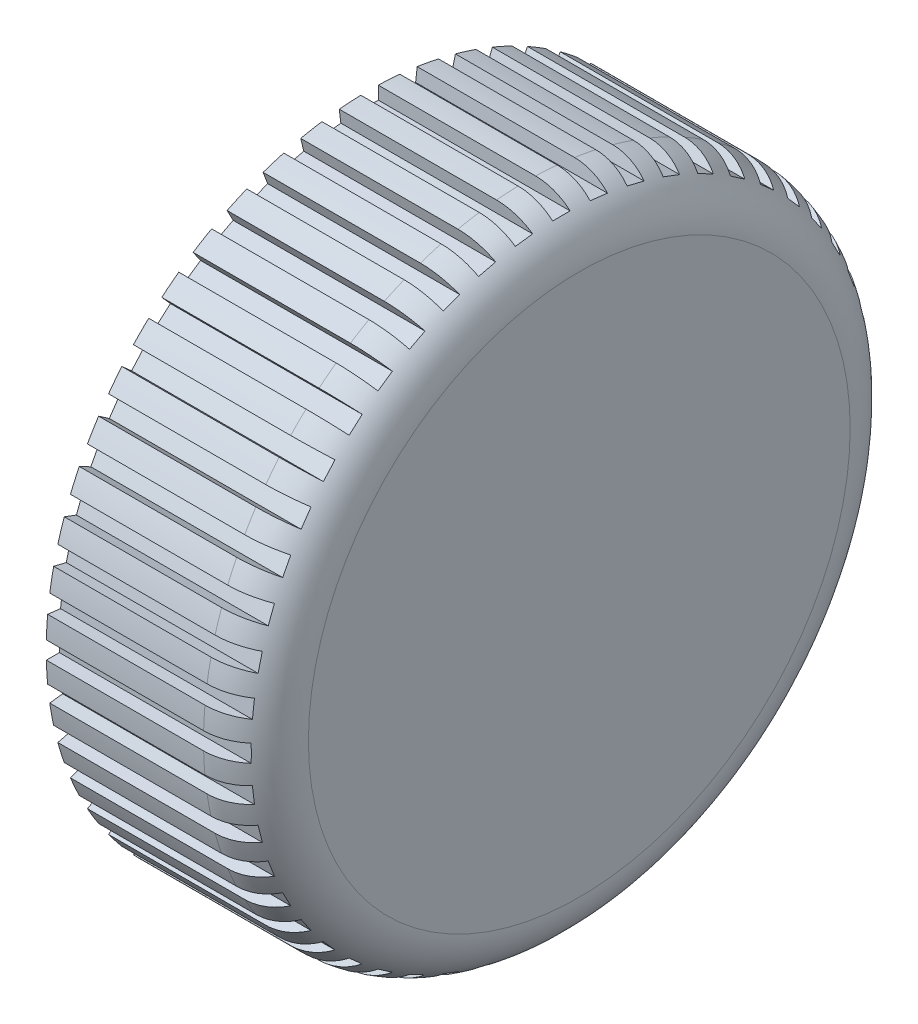
SolidWorks part; units mm, degrees
ref_plane "Спереди" through (0, 0, 0) normal (0, 0, 1) x (1, 0, 0)
ref_plane "Сверху" through (0, 0, 0) normal (0, 1, 0) x (1, 0, 0)
ref_plane "Справа" through (0, 0, 0) normal (1, 0, 0) x (0, 0, -1)
sketch "Эскиз1" plane through (0, 0, 0) normal (0, 0, 1) x (1, 0, 0)
  line L0 (0, 37) -> (0, 30.3)
  line L1 (0, 30.3) -> (16, 30.3)
  line L2 (16, 30.3) -> (16, 0)
  line L3 (16, 0) -> (24, 0)
  line L4 (24, 0) -> (24, 31)
  line L5 (18, 37) -> (0, 37)
  line L6 (0, 30.3) -> (0, 0) construction
  line L7 (0, 0) -> (16, 0) construction
  arc A0 (24, 31) -> (18, 37) centre (18, 31) ccw
  point P11 (0, 0)
  point P12 (0, 0)
  point P13 (0, 0)
  point P14 (16, 0)
  point P15 (16, 0.8492)
  dimension "D6" = 6
  dimension "D1" = 60.6
  dimension "D2" = 74
  dimension "D3" = 8
  dimension "D4" = 16
revolve "Повернуть1" add sketch "Эскиз1" angle 360 about L7
sketch "Эскиз2" plane through (0, 0, 0) normal (-1, 0, 0) x (0, 0, 1)
  line L0 (0, 35.5) -> (0, 0) construction
  line L1 (-1, 38.5) -> (1, 38.5)
  line L2 (-1, 38.5) -> (-1, 35.5)
  line L3 (-1, 35.5) -> (1, 35.5)
  line L4 (1, 38.5) -> (1, 35.5)
  line L5 (5.6334, 38.0988) -> (5.2718, 35.1206)
  line L6 (3.648, 38.3398) -> (3.2863, 35.3617)
  line L7 (3.648, 38.3398) -> (5.6334, 38.0988)
  line L8 (3.2863, 35.3617) -> (5.2718, 35.1206)
  line L9 (10.1846, 37.1419) -> (9.4666, 34.2291)
  line L10 (8.2427, 37.6206) -> (7.5248, 34.7078)
  line L11 (8.2427, 37.6206) -> (10.1846, 37.1419)
  line L12 (7.5248, 34.7078) -> (9.4666, 34.2291)
  line L13 (14.5873, 35.6435) -> (13.5235, 32.8385)
  line L14 (12.7173, 36.3527) -> (11.6535, 33.5477)
  line L15 (12.7173, 36.3527) -> (14.5873, 35.6435)
  line L16 (11.6535, 33.5477) -> (13.5235, 32.8385)
  line L17 (18.7773, 33.6253) -> (17.3831, 30.969)
  line L18 (17.0064, 34.5548) -> (15.6122, 31.8984)
  line L19 (17.0064, 34.5548) -> (18.7773, 33.6253)
  line L20 (15.6122, 31.8984) -> (17.3831, 30.969)
  line L21 (22.6935, 31.1168) -> (20.9893, 28.6479)
  line L22 (21.0475, 32.2529) -> (19.3433, 29.784)
  line L23 (21.0475, 32.2529) -> (22.6935, 31.1168)
  line L24 (19.3433, 29.784) -> (20.9893, 28.6479)
  line L25 (26.2787, 28.1545) -> (24.2894, 25.909)
  line L26 (24.7817, 29.4808) -> (22.7923, 27.2353)
  line L27 (24.7817, 29.4808) -> (26.2787, 28.1545)
  line L28 (22.7923, 27.2353) -> (24.2894, 25.909)
  line L29 (29.4808, 24.7817) -> (27.2353, 22.7923)
  line L30 (28.1545, 26.2787) -> (25.909, 24.2894)
  line L31 (28.1545, 26.2787) -> (29.4808, 24.7817)
  line L32 (25.909, 24.2894) -> (27.2353, 22.7923)
  line L33 (32.2529, 21.0475) -> (29.784, 19.3433)
  line L34 (31.1168, 22.6935) -> (28.6479, 20.9893)
  line L35 (31.1168, 22.6935) -> (32.2529, 21.0475)
  line L36 (28.6479, 20.9893) -> (29.784, 19.3433)
  line L37 (34.5548, 17.0064) -> (31.8984, 15.6122)
  line L38 (33.6253, 18.7773) -> (30.969, 17.3831)
  line L39 (33.6253, 18.7773) -> (34.5548, 17.0064)
  line L40 (30.969, 17.3831) -> (31.8984, 15.6122)
  line L41 (36.3527, 12.7173) -> (33.5477, 11.6535)
  line L42 (35.6435, 14.5873) -> (32.8385, 13.5235)
  line L43 (35.6435, 14.5873) -> (36.3527, 12.7173)
  line L44 (32.8385, 13.5235) -> (33.5477, 11.6535)
  line L45 (37.6206, 8.2427) -> (34.7078, 7.5248)
  line L46 (37.1419, 10.1846) -> (34.2291, 9.4666)
  line L47 (37.1419, 10.1846) -> (37.6206, 8.2427)
  line L48 (34.2291, 9.4666) -> (34.7078, 7.5248)
  line L49 (38.3398, 3.648) -> (35.3617, 3.2863)
  line L50 (38.0988, 5.6334) -> (35.1206, 5.2718)
  line L51 (38.0988, 5.6334) -> (38.3398, 3.648)
  line L52 (35.1206, 5.2718) -> (35.3617, 3.2863)
  line L53 (38.5, -1) -> (35.5, -1)
  line L54 (38.5, 1) -> (35.5, 1)
  line L55 (38.5, 1) -> (38.5, -1)
  line L56 (35.5, 1) -> (35.5, -1)
  line L57 (38.0988, -5.6334) -> (35.1206, -5.2718)
  line L58 (38.3398, -3.648) -> (35.3617, -3.2863)
  line L59 (38.3398, -3.648) -> (38.0988, -5.6334)
  line L60 (35.3617, -3.2863) -> (35.1206, -5.2718)
  line L61 (37.1419, -10.1846) -> (34.2291, -9.4666)
  line L62 (37.6206, -8.2427) -> (34.7078, -7.5248)
  line L63 (37.6206, -8.2427) -> (37.1419, -10.1846)
  line L64 (34.7078, -7.5248) -> (34.2291, -9.4666)
  line L65 (35.6435, -14.5873) -> (32.8385, -13.5235)
  line L66 (36.3527, -12.7173) -> (33.5477, -11.6535)
  line L67 (36.3527, -12.7173) -> (35.6435, -14.5873)
  line L68 (33.5477, -11.6535) -> (32.8385, -13.5235)
  line L69 (33.6253, -18.7773) -> (30.969, -17.3831)
  line L70 (34.5548, -17.0064) -> (31.8984, -15.6122)
  line L71 (34.5548, -17.0064) -> (33.6253, -18.7773)
  line L72 (31.8984, -15.6122) -> (30.969, -17.3831)
  line L73 (31.1168, -22.6935) -> (28.6479, -20.9893)
  line L74 (32.2529, -21.0475) -> (29.784, -19.3433)
  line L75 (32.2529, -21.0475) -> (31.1168, -22.6935)
  line L76 (29.784, -19.3433) -> (28.6479, -20.9893)
  line L77 (28.1545, -26.2787) -> (25.909, -24.2894)
  line L78 (29.4808, -24.7817) -> (27.2353, -22.7923)
  line L79 (29.4808, -24.7817) -> (28.1545, -26.2787)
  line L80 (27.2353, -22.7923) -> (25.909, -24.2894)
  line L81 (24.7817, -29.4808) -> (22.7923, -27.2353)
  line L82 (26.2787, -28.1545) -> (24.2894, -25.909)
  line L83 (26.2787, -28.1545) -> (24.7817, -29.4808)
  line L84 (24.2894, -25.909) -> (22.7923, -27.2353)
  line L85 (21.0475, -32.2529) -> (19.3433, -29.784)
  line L86 (22.6935, -31.1168) -> (20.9893, -28.6479)
  line L87 (22.6935, -31.1168) -> (21.0475, -32.2529)
  line L88 (20.9893, -28.6479) -> (19.3433, -29.784)
  line L89 (17.0064, -34.5548) -> (15.6122, -31.8984)
  line L90 (18.7773, -33.6253) -> (17.3831, -30.969)
  line L91 (18.7773, -33.6253) -> (17.0064, -34.5548)
  line L92 (17.3831, -30.969) -> (15.6122, -31.8984)
  line L93 (12.7173, -36.3527) -> (11.6535, -33.5477)
  line L94 (14.5873, -35.6435) -> (13.5235, -32.8385)
  line L95 (14.5873, -35.6435) -> (12.7173, -36.3527)
  line L96 (13.5235, -32.8385) -> (11.6535, -33.5477)
  line L97 (8.2427, -37.6206) -> (7.5248, -34.7078)
  line L98 (10.1846, -37.1419) -> (9.4666, -34.2291)
  line L99 (10.1846, -37.1419) -> (8.2427, -37.6206)
  line L100 (9.4666, -34.2291) -> (7.5248, -34.7078)
  line L101 (3.648, -38.3398) -> (3.2863, -35.3617)
  line L102 (5.6334, -38.0988) -> (5.2718, -35.1206)
  line L103 (5.6334, -38.0988) -> (3.648, -38.3398)
  line L104 (5.2718, -35.1206) -> (3.2863, -35.3617)
  line L105 (-1, -38.5) -> (-1, -35.5)
  line L106 (1, -38.5) -> (1, -35.5)
  line L107 (1, -38.5) -> (-1, -38.5)
  line L108 (1, -35.5) -> (-1, -35.5)
  line L109 (-5.6334, -38.0988) -> (-5.2718, -35.1206)
  line L110 (-3.648, -38.3398) -> (-3.2863, -35.3617)
  line L111 (-3.648, -38.3398) -> (-5.6334, -38.0988)
  line L112 (-3.2863, -35.3617) -> (-5.2718, -35.1206)
  line L113 (-10.1846, -37.1419) -> (-9.4666, -34.2291)
  line L114 (-8.2427, -37.6206) -> (-7.5248, -34.7078)
  line L115 (-8.2427, -37.6206) -> (-10.1846, -37.1419)
  line L116 (-7.5248, -34.7078) -> (-9.4666, -34.2291)
  line L117 (-14.5873, -35.6435) -> (-13.5235, -32.8385)
  line L118 (-12.7173, -36.3527) -> (-11.6535, -33.5477)
  line L119 (-12.7173, -36.3527) -> (-14.5873, -35.6435)
  line L120 (-11.6535, -33.5477) -> (-13.5235, -32.8385)
  line L121 (-18.7773, -33.6253) -> (-17.3831, -30.969)
  line L122 (-17.0064, -34.5548) -> (-15.6122, -31.8984)
  line L123 (-17.0064, -34.5548) -> (-18.7773, -33.6253)
  line L124 (-15.6122, -31.8984) -> (-17.3831, -30.969)
  line L125 (-22.6935, -31.1168) -> (-20.9893, -28.6479)
  line L126 (-21.0475, -32.2529) -> (-19.3433, -29.784)
  line L127 (-21.0475, -32.2529) -> (-22.6935, -31.1168)
  line L128 (-19.3433, -29.784) -> (-20.9893, -28.6479)
  line L129 (-26.2787, -28.1545) -> (-24.2894, -25.909)
  line L130 (-24.7817, -29.4808) -> (-22.7923, -27.2353)
  line L131 (-24.7817, -29.4808) -> (-26.2787, -28.1545)
  line L132 (-22.7923, -27.2353) -> (-24.2894, -25.909)
  line L133 (-29.4808, -24.7817) -> (-27.2353, -22.7923)
  line L134 (-28.1545, -26.2787) -> (-25.909, -24.2894)
  line L135 (-28.1545, -26.2787) -> (-29.4808, -24.7817)
  line L136 (-25.909, -24.2894) -> (-27.2353, -22.7923)
  line L137 (-32.2529, -21.0475) -> (-29.784, -19.3433)
  line L138 (-31.1168, -22.6935) -> (-28.6479, -20.9893)
  line L139 (-31.1168, -22.6935) -> (-32.2529, -21.0475)
  line L140 (-28.6479, -20.9893) -> (-29.784, -19.3433)
  line L141 (-34.5548, -17.0064) -> (-31.8984, -15.6122)
  line L142 (-33.6253, -18.7773) -> (-30.969, -17.3831)
  line L143 (-33.6253, -18.7773) -> (-34.5548, -17.0064)
  line L144 (-30.969, -17.3831) -> (-31.8984, -15.6122)
  line L145 (-36.3527, -12.7173) -> (-33.5477, -11.6535)
  line L146 (-35.6435, -14.5873) -> (-32.8385, -13.5235)
  line L147 (-35.6435, -14.5873) -> (-36.3527, -12.7173)
  line L148 (-32.8385, -13.5235) -> (-33.5477, -11.6535)
  line L149 (-37.6206, -8.2427) -> (-34.7078, -7.5248)
  line L150 (-37.1419, -10.1846) -> (-34.2291, -9.4666)
  line L151 (-37.1419, -10.1846) -> (-37.6206, -8.2427)
  line L152 (-34.2291, -9.4666) -> (-34.7078, -7.5248)
  line L153 (-38.3398, -3.648) -> (-35.3617, -3.2863)
  line L154 (-38.0988, -5.6334) -> (-35.1206, -5.2718)
  line L155 (-38.0988, -5.6334) -> (-38.3398, -3.648)
  line L156 (-35.1206, -5.2718) -> (-35.3617, -3.2863)
  line L157 (-38.5, 1) -> (-35.5, 1)
  line L158 (-38.5, -1) -> (-35.5, -1)
  line L159 (-38.5, -1) -> (-38.5, 1)
  line L160 (-35.5, -1) -> (-35.5, 1)
  line L161 (-38.0988, 5.6334) -> (-35.1206, 5.2718)
  line L162 (-38.3398, 3.648) -> (-35.3617, 3.2863)
  line L163 (-38.3398, 3.648) -> (-38.0988, 5.6334)
  line L164 (-35.3617, 3.2863) -> (-35.1206, 5.2718)
  line L165 (-37.1419, 10.1846) -> (-34.2291, 9.4666)
  line L166 (-37.6206, 8.2427) -> (-34.7078, 7.5248)
  line L167 (-37.6206, 8.2427) -> (-37.1419, 10.1846)
  line L168 (-34.7078, 7.5248) -> (-34.2291, 9.4666)
  line L169 (-35.6435, 14.5873) -> (-32.8385, 13.5235)
  line L170 (-36.3527, 12.7173) -> (-33.5477, 11.6535)
  line L171 (-36.3527, 12.7173) -> (-35.6435, 14.5873)
  line L172 (-33.5477, 11.6535) -> (-32.8385, 13.5235)
  line L173 (-33.6253, 18.7773) -> (-30.969, 17.3831)
  line L174 (-34.5548, 17.0064) -> (-31.8984, 15.6122)
  line L175 (-34.5548, 17.0064) -> (-33.6253, 18.7773)
  line L176 (-31.8984, 15.6122) -> (-30.969, 17.3831)
  line L177 (-31.1168, 22.6935) -> (-28.6479, 20.9893)
  line L178 (-32.2529, 21.0475) -> (-29.784, 19.3433)
  line L179 (-32.2529, 21.0475) -> (-31.1168, 22.6935)
  line L180 (-29.784, 19.3433) -> (-28.6479, 20.9893)
  line L181 (-28.1545, 26.2787) -> (-25.909, 24.2894)
  line L182 (-29.4808, 24.7817) -> (-27.2353, 22.7923)
  line L183 (-29.4808, 24.7817) -> (-28.1545, 26.2787)
  line L184 (-27.2353, 22.7923) -> (-25.909, 24.2894)
  line L185 (-24.7817, 29.4808) -> (-22.7923, 27.2353)
  line L186 (-26.2787, 28.1545) -> (-24.2894, 25.909)
  line L187 (-26.2787, 28.1545) -> (-24.7817, 29.4808)
  line L188 (-24.2894, 25.909) -> (-22.7923, 27.2353)
  line L189 (-21.0475, 32.2529) -> (-19.3433, 29.784)
  line L190 (-22.6935, 31.1168) -> (-20.9893, 28.6479)
  line L191 (-22.6935, 31.1168) -> (-21.0475, 32.2529)
  line L192 (-20.9893, 28.6479) -> (-19.3433, 29.784)
  line L193 (-17.0064, 34.5548) -> (-15.6122, 31.8984)
  line L194 (-18.7773, 33.6253) -> (-17.3831, 30.969)
  line L195 (-18.7773, 33.6253) -> (-17.0064, 34.5548)
  line L196 (-17.3831, 30.969) -> (-15.6122, 31.8984)
  line L197 (-12.7173, 36.3527) -> (-11.6535, 33.5477)
  line L198 (-14.5873, 35.6435) -> (-13.5235, 32.8385)
  line L199 (-14.5873, 35.6435) -> (-12.7173, 36.3527)
  line L200 (-13.5235, 32.8385) -> (-11.6535, 33.5477)
  line L201 (-8.2427, 37.6206) -> (-7.5248, 34.7078)
  line L202 (-10.1846, 37.1419) -> (-9.4666, 34.2291)
  line L203 (-10.1846, 37.1419) -> (-8.2427, 37.6206)
  line L204 (-9.4666, 34.2291) -> (-7.5248, 34.7078)
  line L205 (-3.648, 38.3398) -> (-3.2863, 35.3617)
  line L206 (-5.6334, 38.0988) -> (-5.2718, 35.1206)
  line L207 (-5.6334, 38.0988) -> (-3.648, 38.3398)
  line L208 (-5.2718, 35.1206) -> (-3.2863, 35.3617)
  point P213 (0, 0)
  dimension "D1" = 2
  dimension "D2" = 35.5
  dimension "D3" = 3
extrude "Вырез-Вытянуть2" cut sketch "Эскиз2" against normal through all
